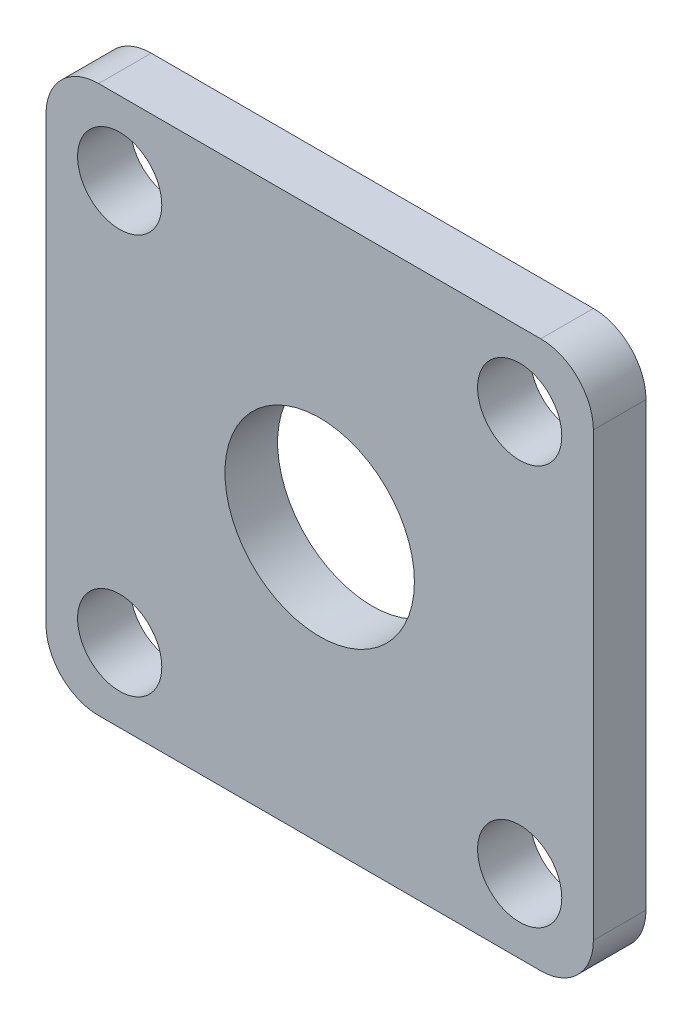
SolidWorks part; units mm, degrees
material "Acciaio al carbonio semplice"
ref_plane "Piano frontale" through (0, 0, 0) normal (0, 0, 1) x (1, 0, 0)
ref_plane "Piano superiore" through (0, 0, 0) normal (0, 1, 0) x (1, 0, 0)
ref_plane "Piano destro" through (0, 0, 0) normal (1, 0, 0) x (0, 0, -1)
sketch "Schizzo1" plane through (0, 0, 0) normal (0, 0, 1) x (1, 0, 0)
  line L0 (26, 57.5561) -> (26, -10.6306) construction
  line L1 (5, 52) -> (47, 52)
  line L2 (0, 47) -> (0, 5)
  line L3 (5, 0) -> (47, 0)
  line L4 (52, 47) -> (52, 5)
  line L5 (-11.3051, 26) -> (68.5953, 26) construction
  circle A0 centre (7, 45) radius 4
  circle A1 centre (45, 45) radius 4
  circle A2 centre (7, 7) radius 4
  circle A3 centre (45, 7) radius 4
  arc A4 (0, 5) -> (5, 0) centre (5, 5) ccw
  arc A5 (47, 0) -> (52, 5) centre (47, 5) ccw
  arc A6 (47, 52) -> (52, 47) centre (47, 47) cw
  arc A7 (5, 52) -> (0, 47) centre (5, 47) ccw
  circle A8 centre (26, 26) radius 9
  point P19 (0, 0)
  point P22 (52, 0)
  point P25 (52, 52)
  point P28 (0, 52)
  dimension "D3" = 8
  dimension "D6" = 38
  dimension "D7" = 38
  dimension "D8" = 5
  dimension "D9" = 18
  dimension "D1" = 52
  dimension "D2" = 52
  dimension "D4" = 2
  dimension "D5" = 2
extrude "Estrusione-Estrusione1" add sketch "Schizzo1" along normal blind 5
